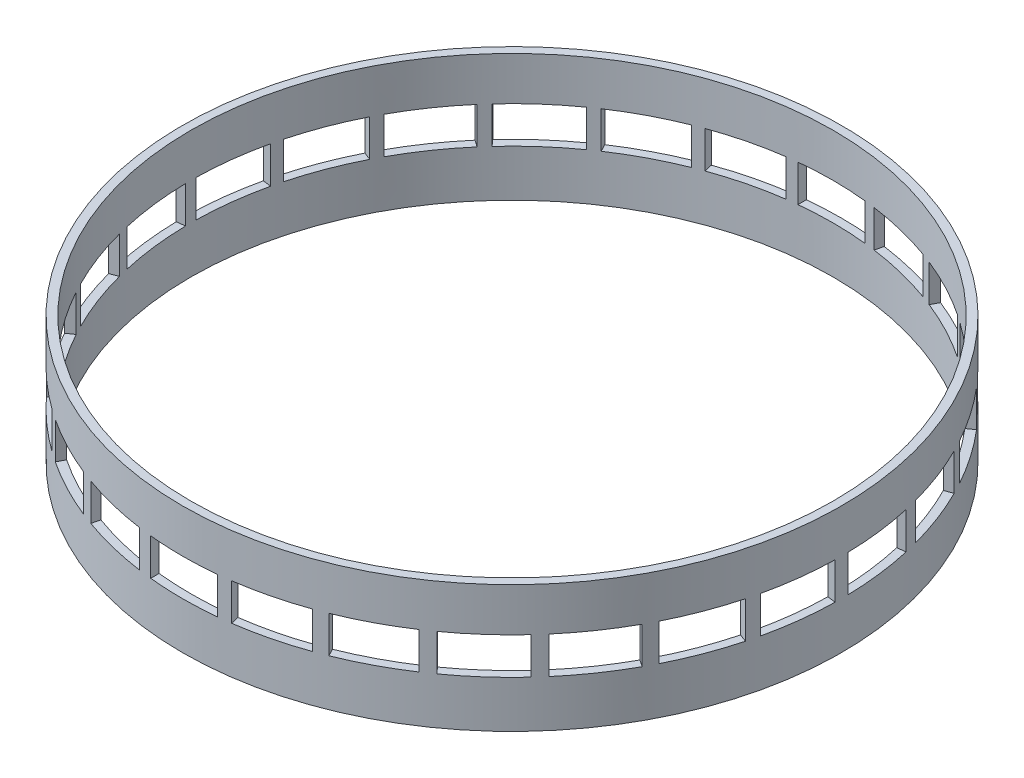
SolidWorks part; units mm, degrees
material "ABS PC"
ref_plane "Front" through (0, 0, 0) normal (0, 0, 1) x (1, 0, 0)
ref_plane "Top" through (0, 0, 0) normal (0, 1, 0) x (1, 0, 0)
ref_plane "Right" through (0, 0, 0) normal (1, 0, 0) x (0, 0, -1)
sketch "Sketch1" plane through (0, 0, 0) normal (0, 1, 0) x (1, 0, 0)
  circle A0 centre (0, 0) radius 96
  circle A1 centre (0, 0) radius 98.5
  dimension "D1" = 197
  dimension "D2" = 192
extrude "Boss-Extrude1" add sketch "Sketch1" along normal blind 38
sketch "Sketch2" plane through (0, 0, 0) normal (0, 0, 1) x (1, 0, 0)
  line L1 (-10, 25) -> (10, 25)
  line L2 (-10, 25) -> (-10, 14)
  line L3 (-10, 14) -> (10, 14)
  line L4 (10, 25) -> (10, 14)
  line L5 (-98.5, 0) -> (98.5, 0) construction
  line L6 (-96, 0) -> (96, 0) construction
  line L7 (0, 0) -> (0, 25) construction
  dimension "D1" = 14
  dimension "D2" = 11
  dimension "D3" = 20
extrude "Cut-Extrude1" cut sketch "Sketch2" against normal through all both and the other way through all
pattern_circular "CirPattern1" count 13 over 360 about axis through (0, 0, 0) along (0, 1, 0) of "Cut-Extrude1"
